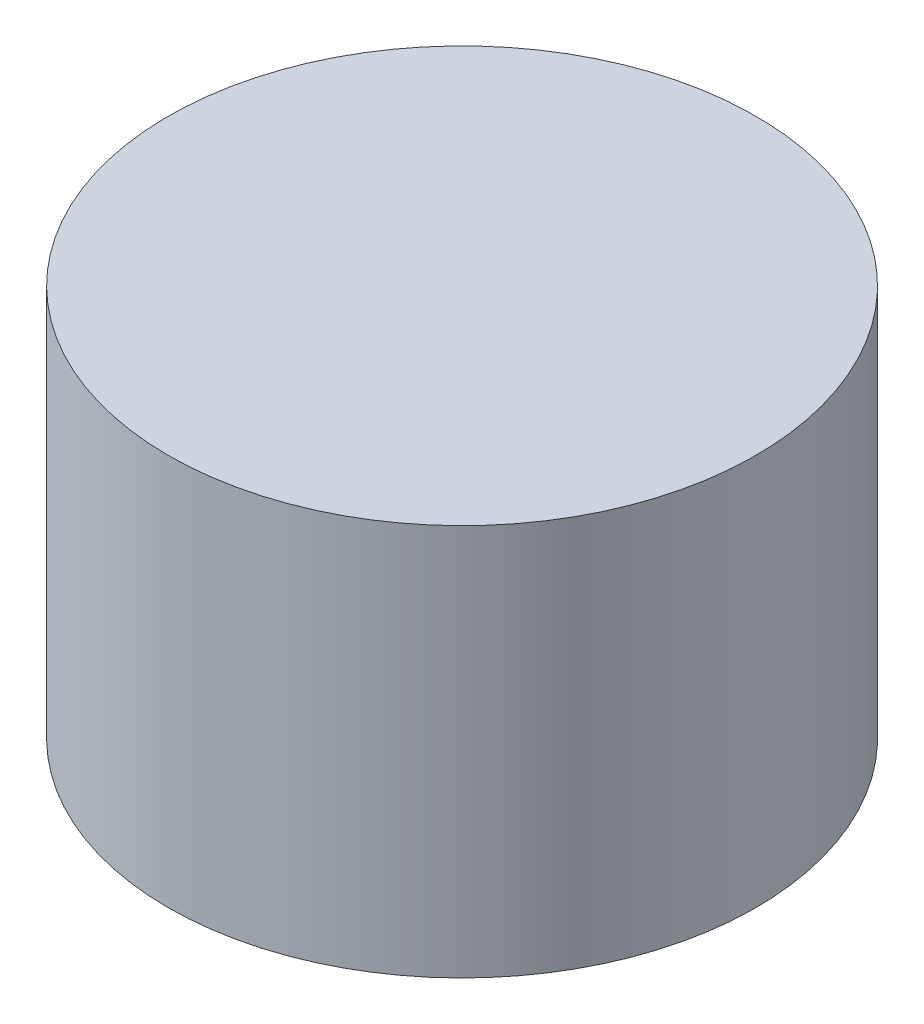
SolidWorks part; units mm, degrees
ref_plane "Front Plane" through (0, 0, 0) normal (0, 0, 1) x (1, 0, 0)
ref_plane "Top Plane" through (0, 0, 0) normal (0, 1, 0) x (1, 0, 0)
ref_plane "Right Plane" through (0, 0, 0) normal (1, 0, 0) x (0, 0, -1)
sketch "Sketch1" plane through (0, 0, 0) normal (0, 1, 0) x (1, 0, 0)
  circle A0 centre (0, 0) radius 4.5
extrude "Boss-Extrude1" add sketch "Sketch1" along normal blind 6
